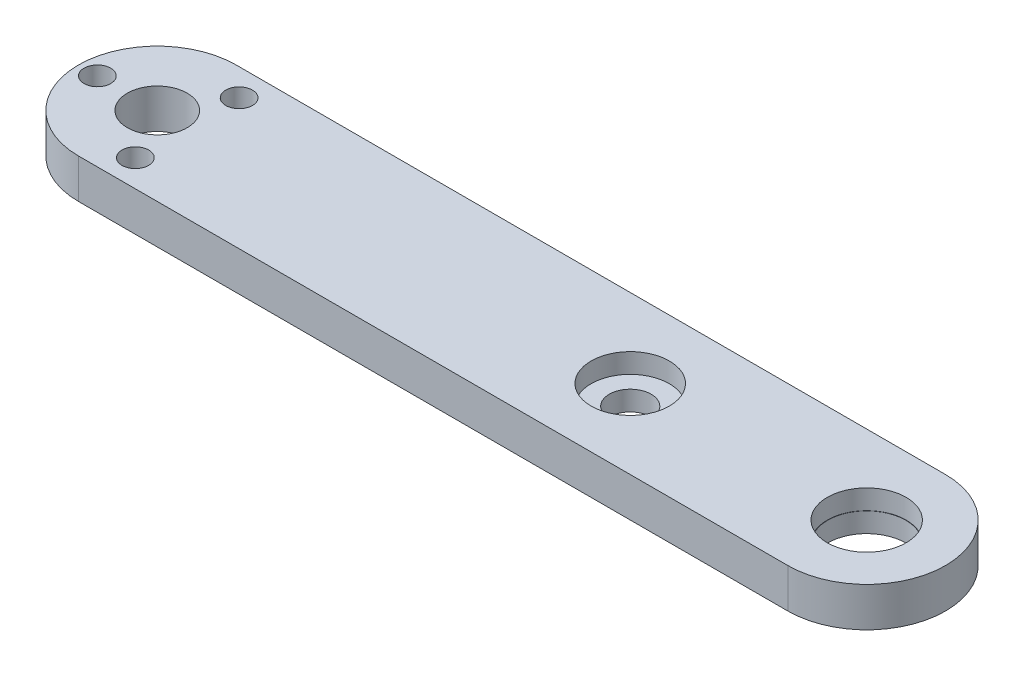
SolidWorks part; units mm, degrees
ref_plane "Front Plane" through (0, 0, 0) normal (0, 0, 1) x (1, 0, 0)
ref_plane "Top Plane" through (0, 0, 0) normal (0, 1, 0) x (1, 0, 0)
ref_plane "Right Plane" through (0, 0, 0) normal (1, 0, 0) x (0, 0, -1)
sketch "Sketch1" plane through (0, 0, 0) normal (0, 1, 0) x (1, 0, 0)
  line L0 (0, 12.7) -> (114.3, 12.7)
  line L1 (114.3, 12.7) -> (114.3, -12.7) construction
  line L2 (114.3, -12.7) -> (0, -12.7)
  arc A0 (0, 12.7) -> (0, -12.7) centre (0, 0) ccw
  arc A1 (114.3, -12.7) -> (114.3, 12.7) centre (114.3, 0) ccw
  circle A2 centre (0, 0) radius 4.826
  dimension "D1" = 12.7
  dimension "D2" = 9.652
  dimension "D3" = 114.3
  dimension "D4" = 114.3
extrude "Boss-Extrude1" add sketch "Sketch1" along normal blind 6.35
hole_wizard "#18 (0.1695) Diameter Hole1" positions "Sketch3" profile "Sketch2" hole size "#18" standard "ANSI Inch"
sketch "Sketch3" plane through (0, 6.35, 0) normal (0, 1, 0) x (1, 0, 0)
  line L0 (0, 0) -> (-12.7, 0) construction
  line L3 (0, 0) -> (7.3323, 12.7) construction
  line L4 (114.3, 12.7) -> (0, 12.7) construction
  arc A0 (0, 12.7) -> (0, -12.7) centre (0, 0) ccw construction
  point P23 (-9.652, 0)
  point P25 (4.826, 8.3589)
  point P28 (4.826, -8.3589)
  dimension "D1" = 120
  dimension "D2" = 9.652
  dimension "D3" = 9.652
sketch "Sketch2" plane through (-9.652, 6.35, 0) normal (1, 0, 0) x (0, 0, 1)
  line L0 (0, 0) -> (0, 26.6934)
  line L1 (0, 26.6934) -> (2.1526, 25.4)
  line L2 (2.1526, 25.4) -> (2.1526, 0)
  line L5 (2.1526, 0) -> (0, 0)
  line L10 (0, 26.6934) -> (-2.1527, 25.4) construction
  line L11 (0, -6.35) -> (0, 107.95) construction
  dimension "Hole Dia." = 4.3053
  dimension "Hole Depth" = 25.4
  dimension "Drill Angle" = 118
sketch "Sketch4" plane through (0, 6.35, 0) normal (0, 1, 0) x (1, 0, 0)
  line L0 (0, 0) -> (76.2, 0) construction
  circle A0 centre (76.2, 0) radius 6.2992
  circle A1 centre (114.3, 0) radius 6.35
  dimension "D2" = 12.5984
  dimension "D3" = 12.7
  dimension "D1" = 76.2
extrude "Cut-Extrude1" cut sketch "Sketch4" against normal blind 3.175
sketch "Sketch5" plane through (0, 0, 0) normal (0, -1, 0) x (1, 0, 0)
  line L0 (0, 0) -> (114.3, 0) construction
  circle A0 centre (114.3, 0) radius 6.2992
  dimension "D1" = 12.5984
  dimension "D2" = 114.3
extrude "Cut-Extrude2" cut sketch "Sketch5" against normal blind 3.175
hole_wizard "17/64 (0.26563) Diameter Hole1" positions "Sketch7" profile "Sketch8" hole size "17/64" standard "ANSI Inch" end condition through all
sketch "Sketch7" plane through (0, 6.35, 0) normal (0, 1, 0) x (1, 0, 0)
  line L2 (0, 0) -> (114.3, 0) construction
  point P11 (76.2, 0)
  point P13 (114.3, 0)
  dimension "D1" = 76.2
  dimension "D2" = 114.3
sketch "Sketch8" plane through (76.2, 6.35, 0) normal (1, 0, 0) x (0, 0, 1)
  line L0 (0, 0) -> (0, 6.35)
  line L1 (0, 6.35) -> (3.3735, 6.35)
  line L2 (3.3735, 6.35) -> (3.3735, 0)
  line L5 (3.3735, 0) -> (0, 0)
  line L11 (0, -6.35) -> (0, 107.95) construction
  dimension "Thru Hole Dia." = 6.747
  dimension "Thru Hole Depth" = 6.35
hole_wizard "#47 (0.0785) Diameter Hole1" [suppressed] positions "Sketch11" profile "Sketch10" hole size "#47" standard "ANSI Inch"
sketch "Sketch11" [suppressed] plane through (0, 6.35, 0) normal (0, 1, 0) x (1, 0, 0)
  line L0 (76.2, 0) -> (114.3, 0) construction
  line L7 (114.3, 0) -> (114.3, 12.7) construction
  point P26 (114.3, 7.4422)
  point P29 (114.3, -7.4422)
  dimension "D1" = 7.4422
sketch "Sketch10" plane through (114.3, 6.35, -7.4422) normal (1, 0, 0) x (0, 0, 1)
  line L0 (0, 0) -> (0, 3.774)
  line L1 (0, 3.774) -> (0.9969, 3.175)
  line L2 (0.9969, 3.175) -> (0.9969, 0)
  line L5 (0.9969, 0) -> (0, 0)
  line L10 (0, 3.774) -> (-0.997, 3.175) construction
  line L11 (0, -6.35) -> (0, 107.95) construction
  dimension "Hole Dia." = 1.9939
  dimension "Hole Depth" = 3.175
  dimension "Drill Angle" = 118
hole_wizard "#47 (0.0785) Diameter Hole2" [suppressed] positions "Sketch13" profile "Sketch12" hole size "#47" standard "ANSI Inch"
sketch "Sketch13" [suppressed] plane through (0, 0, 0) normal (0, -1, 0) x (-1, 0, 0)
  line L0 (-76.2, 0) -> (-76.2, -12.7) construction
  line L1 (0, -12.7) -> (-114.3, -12.7) construction
  line L4 (-76.2, 0) -> (-73.0606, 0) construction
  point P16 (-76.2, -7.4422)
  point P19 (-76.2, 7.4422)
  dimension "D1" = 7.4422
sketch "Sketch12" plane through (76.2, 0, 7.4422) normal (1, 0, 0) x (0, 0, -1)
  line L0 (0, 0) -> (0, 3.774)
  line L1 (0, 3.774) -> (0.9969, 3.175)
  line L2 (0.9969, 3.175) -> (0.9969, 0)
  line L5 (0.9969, 0) -> (0, 0)
  line L10 (0, 3.774) -> (-0.997, 3.175) construction
  line L11 (0, -6.35) -> (0, 107.95) construction
  dimension "Hole Dia." = 1.9939
  dimension "Hole Depth" = 3.175
  dimension "Drill Angle" = 118
sketch "Sketch14" plane through (0, 6.35, 0) normal (0, 1, 0) x (1, 0, 0)
equation "\"D4@Sketch1\"=\"D3@Sketch1\""
